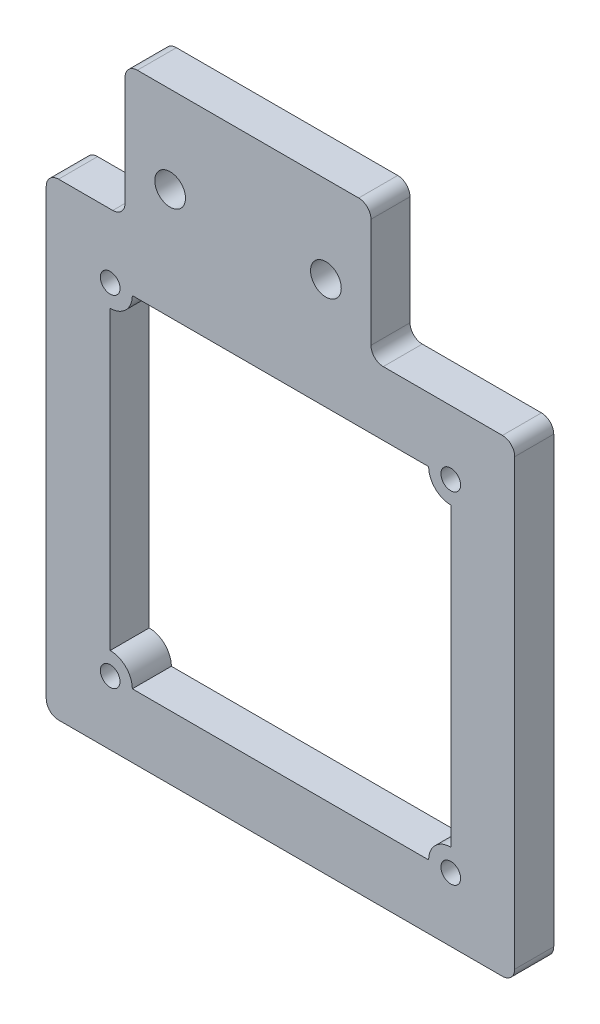
SolidWorks part; units mm, degrees
ref_plane "Front Plane" through (0, 0, 0) normal (0, 0, 1) x (1, 0, 0)
ref_plane "Top Plane" through (0, 0, 0) normal (0, 1, 0) x (1, 0, 0)
ref_plane "Right Plane" through (0, 0, 0) normal (1, 0, 0) x (0, 0, -1)
sketch "Sketch1" plane through (0, 0, 0) normal (0, 0, 1) x (1, 0, 0)
  line L0 (31.6909, -38.1) -> (31.6909, 0) construction
  line L1 (-6.4091, -38.1) -> (31.6909, -38.1) construction
  line L2 (-6.4091, 0) -> (-6.4091, -38.1) construction
  line L3 (31.6909, 0) -> (-6.4091, 0) construction
  line L4 (0, 14.3492) -> (0, 0) construction
  line L5 (16.335, 3.8116) -> (20, 3.8116) construction
  line L6 (20, 14.3492) -> (20, 0) construction
  line L7 (31.6909, -38.1) -> (31.6909, 0)
  line L8 (-6.4091, -38.1) -> (31.6909, -38.1)
  line L9 (-6.4091, 0) -> (-6.4091, -38.1)
  line L10 (31.6909, 0) -> (20, 0)
  line L11 (0, 10.8755) -> (0, 0)
  line L12 (3.665, 3.8116) -> (0, 3.8116) construction
  line L13 (20, 10.8755) -> (20, 0)
  line L14 (0, 0) -> (-6.4091, 0)
  line L15 (20, 10.8755) -> (0, 10.8755)
  line L16 (10, 10.8755) -> (10, -38.1) construction
  line L17 (26.4909, -7) -> (26.4909, -31.1)
  line L18 (24.6909, -32.9) -> (0.5909, -32.9)
  line L19 (-1.2091, -7) -> (-1.2091, -31.1)
  line L22 (24.6909, -5.2) -> (0.5909, -5.2)
  circle A3 centre (-1.2091, -5.2) radius 0.7556 construction
  circle A4 centre (26.4909, -32.9) radius 0.8
  circle A5 centre (-1.2091, -32.9) radius 0.8
  circle A6 centre (-1.2091, -5.2) radius 0.8
  circle A7 centre (26.4909, -5.2) radius 0.8
  circle A8 centre (16.335, 3.8116) radius 1.25
  circle A9 centre (3.665, 3.8116) radius 1.25
  arc A10 (26.4909, -7) -> (24.6909, -5.2) centre (26.4909, -5.2) cw
  arc A11 (26.4909, -31.1) -> (24.6909, -32.9) centre (26.4909, -32.9) ccw
  arc A12 (0.5909, -32.9) -> (-1.2091, -31.1) centre (-1.2091, -32.9) ccw
  arc A13 (-1.2091, -7) -> (0.5909, -5.2) centre (-1.2091, -5.2) ccw
  circle A15 centre (-1.2091, -32.9) radius 0.7556 construction
  circle A16 centre (26.4909, -32.9) radius 0.9271 construction
  dimension "D1" = 2.5
  dimension "D2" = 1
  dimension "D3" = 1.6
extrude "Boss-Extrude1" add sketch "Sketch1" along normal blind 3.175 contours A5 | A4 | A9 | L13 L10 L7 L8 L9 L14 L11 L15 | L19 A12 L18 A11 L17 A10 L22 A13 | A7 | A6 | A8
fillet "Fillet1" radius 1 8 edges at (20, 0, 1.5875) (20, 10.8755, 1.5875) (0, 10.8755, 1.5875) (0, 0, 1.5875) (-6.4091, 0, 1.5875) (-6.4091, -38.1, 1.5875) (31.6909, 0, 1.5875) (31.6909, -38.1, 1.5875)
